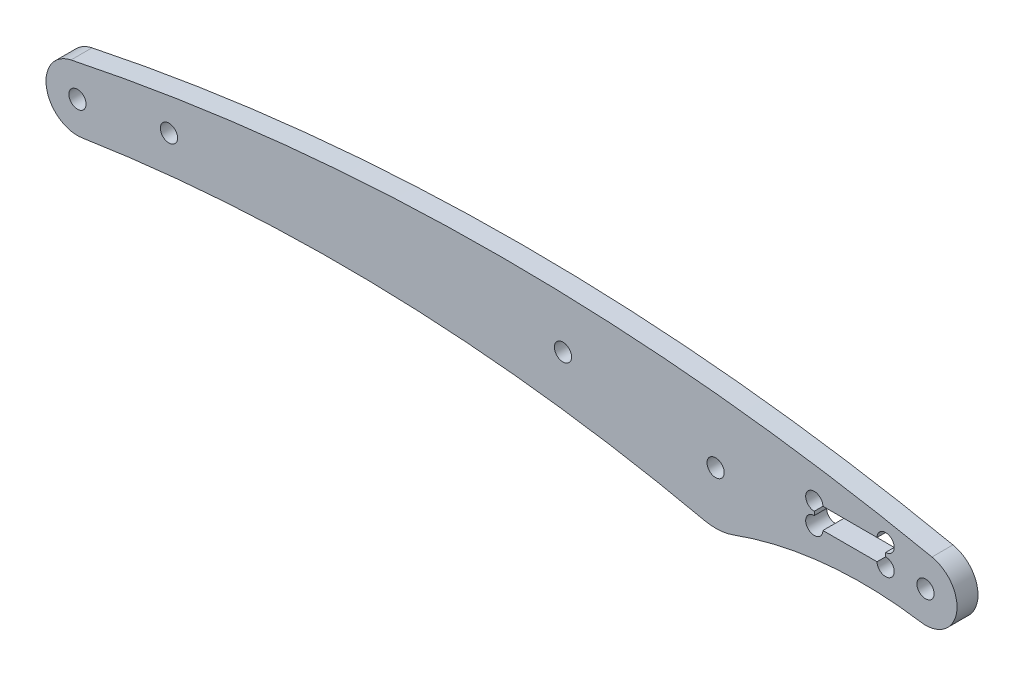
SolidWorks part; units mm, degrees
material "Acrílico (Impacto medio-alto)"
ref_plane "Piano frontale" through (0, 0, 0) normal (0, 0, 1) x (1, 0, 0)
ref_plane "Piano superiore" through (0, 0, 0) normal (0, 1, 0) x (1, 0, 0)
ref_plane "Piano destro" through (0, 0, 0) normal (1, 0, 0) x (0, 0, -1)
sketch "Schizzo1" plane through (0, 0, 0) normal (0, 0, 1) x (1, 0, 0)
  line L0 (0, 0) -> (152, 0) construction
  line L1 (152, 0) -> (202, 0) construction
  circle A0 centre (0, 0) radius 2.05
  circle A1 centre (202, 0) radius 2.05
  arc A2 (-1.5381, 7.3406) -> (1.1505, -7.4112) centre (0, 0) ccw
  arc A3 (200.8462, -7.4107) -> (203.5381, 7.3406) centre (202, 0) ccw
  circle A4 centre (152, 0) radius 2.05
  arc A5 (149.2883, -12.2023) -> (156.2683, -11.7487) centre (152, 0) ccw
  arc A6 (149.2883, -12.2023) -> (1.1505, -7.4112) centre (62.5132, -402.6765) ccw
  arc A7 (203.5381, 7.3406) -> (-1.5381, 7.3406) centre (101, -482.0324) ccw
  arc A8 (200.8462, -7.4107) -> (156.2683, -11.7487) centre (187, -96.3392) ccw
  dimension "D1" = 4.1
  dimension "D4" = 15
  dimension "D5" = 15
  dimension "D8" = 25
  dimension "D9" = 800
  dimension "D10" = 1000
  dimension "D11" = 152
  dimension "D12" = 90
  dimension "D3" = 202
extrude "Estrusione-Estrusione1" add sketch "Schizzo1" along normal blind 5
sketch "Schizzo2" plane through (0, 0, 5) normal (0, 0, 1) x (1, 0, 0)
  circle A0 centre (21.7926, 3.9239) radius 2.05
  circle A1 centre (115.6435, 5.6739) radius 2.05
  dimension "D3" = 4.1
extrude "Taglio-Estrusione1" cut sketch "Schizzo2" against normal blind 10
sketch "Sketch1" plane through (0, 0, 5) normal (0, 0, 1) x (1, 0, 0)
  line L0 (184, -6.3893) -> (184, 11.0305) construction
  line L1 (175.5, -0.1794) -> (192.5, -0.1794)
  line L2 (175.5, -0.1794) -> (175.5, 4.8206)
  line L3 (175.5, 4.8206) -> (192.5, 4.8206)
  line L4 (192.5, -0.1794) -> (192.5, 4.8206)
  line L5 (175.5, -0.1794) -> (192.5, 4.8206) construction
  line L6 (175.5, 4.8206) -> (192.5, -0.1794) construction
  arc A0 (200.8462, -7.4107) -> (156.2683, -11.7487) centre (187, -96.3392) ccw construction
  arc A1 (203.5381, 7.3406) -> (-1.5381, 7.3406) centre (101, -482.0324) ccw construction
  point P4 (184, 2.3206)
  point P13 (202, 0)
  dimension "D1" = 5
  dimension "D2" = 17
  dimension "D3" = 18
extrude "Cut-Extrude1" cut sketch "Sketch1" against normal up to next
sketch "Sketch2" plane through (0, 0, 5) normal (0, 0, 1) x (1, 0, 0)
  circle A0 centre (175.5, 4.8206) radius 2.05
  circle A1 centre (175.5, -0.1794) radius 2.05
  circle A2 centre (192.5, -0.1794) radius 2.05
  circle A3 centre (192.5, 4.8206) radius 2.05
  dimension "D1" = 4.1
extrude "Cut-Extrude2" cut sketch "Sketch2" against normal up to next
